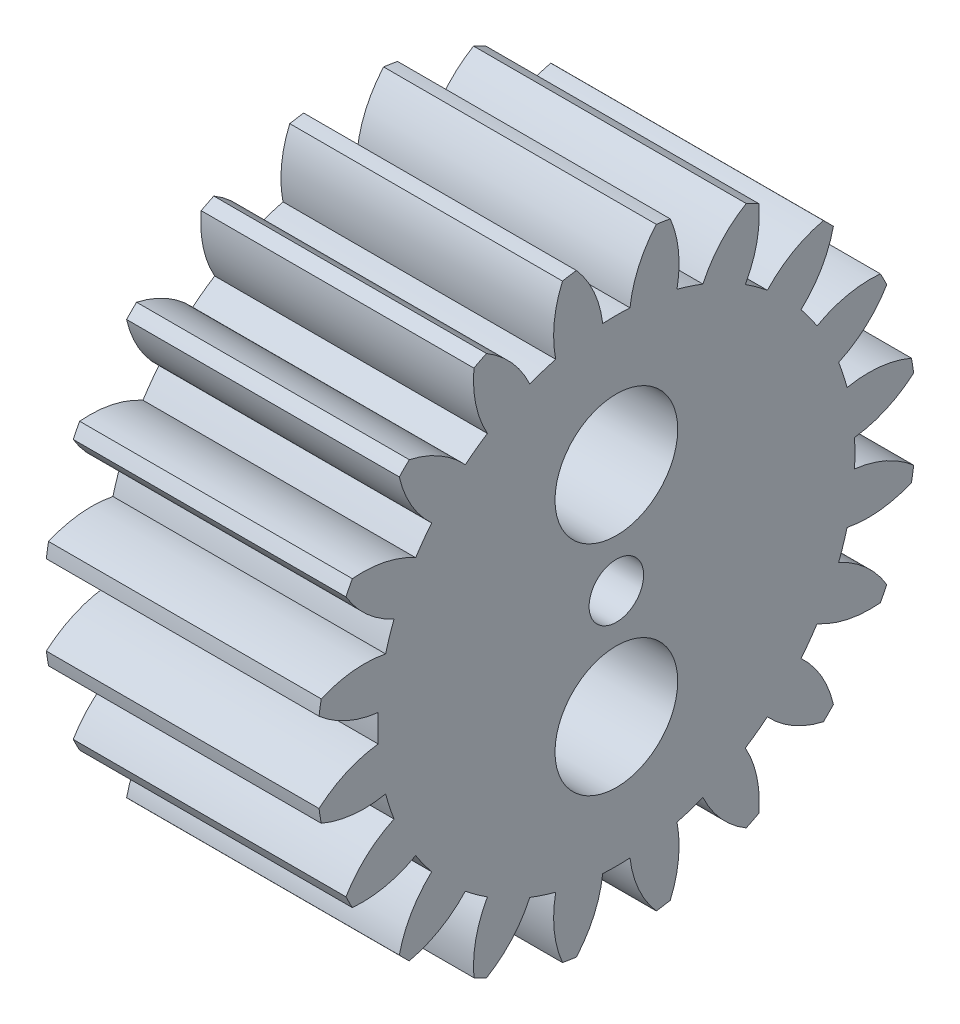
SolidWorks part; units mm, degrees
ref_plane "Plane1" through (0, 0, 0) normal (0, 0, 1) x (1, 0, 0)
ref_plane "Plane2" through (0, 0, 0) normal (0, 1, 0) x (1, 0, 0)
ref_plane "Plane3" through (0, 0, 0) normal (1, 0, 0) x (0, 0, -1)
sketch "HoldingSke" plane through (0, 0, 0) normal (0, 1, 0) x (1, 0, 0)
  line L0 (0, 0) -> (1.8794, -0.684)
  line L1 (-15, 0) -> (100, 0) construction
  line L2 (0, 0) -> (-2.1039, 2.3779)
  line L3 (0, 0) -> (-11.863, 4.5341)
  line L4 (0, 0) -> (8.1152, 2.9537)
  line L5 (0, 0) -> (-46.8476, -17.4728)
  line L6 (0, 0) -> (-4.1448, -2.7965)
  line L7 (-2.1039, 2.3779) -> (8.6586, 51.2059)
  line L8 (-76.2, 54.61) -> (-76.1, 54.61)
  line L9 (-71.009, 38.7566) -> (-53.1078, 45.2721)
  line L10 (-76.2, 71.12) -> (104.1128, 71.12)
  line L11 (0, 0) -> (-5, 0)
  line L12 (-76.2, 101.6) -> (-76.181, 101.6)
  line L13 (24.9733, 27.94) -> (52.9518, 28.4284)
  line L14 (24.9733, 27.94) -> (24.9743, 27.94)
  line L15 (24.9733, 27.94) -> (100.4006, 29.5858)
  line L16 (-63.627, -0.5) -> (-12.827, -0.5)
  circle A0 centre (0, 0) radius 0.5
  circle A1 centre (0, 0) radius 4.374
  circle A2 centre (0, 0) radius 37.5
  circle A3 centre (0, 0) radius 0.5
  dimension "MHD" = 8.748
  dimension "Hub_dia" = 75
  dimension "Bore" = 1
  dimension "MBD" = 1
  dimension "Num_teeth" = 20
  dimension "Pitch" = 2
  dimension "Overall_len" = 50
  dimension "Show_teeth" = 20
  dimension "Thickness" = 5
  dimension "OAL" = 50.0001
  dimension "T_dim" = 0.1
  dimension "Ap" = 20
  dimension "H" = 19.05
  dimension "Pitch_radius" = 180.3128
  dimension "Width" = 5
  dimension "Backlash" = 0.019
  dimension "Addendum_fac" = 1
  dimension "Dedendum_fac" = 1.25
  dimension "Clearance_fac" = 0.25
  dimension "Dedendum_add" = 0.001
  dimension "Module" = 0.5
sketch "BasProSke" plane through (0, 0, 0) normal (0, 1, 0) x (1, 0, 0)
  line L0 (-10, 0) -> (60, 0) construction
  line L1 (0, 0) -> (0, 5.5)
  line L2 (0, 0) -> (5, 0)
  line L3 (5, 0) -> (5, 5.5)
  line L4 (5, 5.5) -> (0, 5.5)
  dimension "Thickness" = 5
  dimension "Diameter" = 11
revolve "Base-Revolve" add sketch "BasProSke" angle 360 about L0
sketch "TooCutSke" plane through (0, 0, 0) normal (1, 0, 0) x (0, 0, -1)
  line L1 (0, 0) -> (0, 107) construction
  line L2 (0, 0) -> (-0.4255, 4.9819) construction
  line L3 (0, 0) -> (-1.5603, 9.8514) construction
  line L4 (-0.4255, 4.9819) -> (-0.7802, 4.9257) construction
  arc A0 (0.2499, 4.3669) -> (-0.2499, 4.3669) centre (0, 0) ccw
  arc A1 (0.7528, 5.4739) -> (-0.7528, 5.4739) centre (0, 0) ccw
  circle A2 centre (0, 0) radius 5 construction
  circle A3 centre (0, 0) radius 4.6985 construction
  arc A4 (-0.2499, 4.3669) -> (-0.7528, 5.4739) centre (-2.2361, 4.1322) ccw
  arc A5 (0.7528, 5.4739) -> (0.2499, 4.3669) centre (2.2361, 4.1322) ccw
  dimension "Root_dia" = 8.748
  dimension "Overcut_dia" = 11.0508
  dimension "Pitch_dia" = 10
  dimension "Base_dia" = 9.3969
  dimension "Flank_rad" = 2
  dimension "Half_ang" = 9
  dimension "Half_CT" = 0.359
extrude "ToothCut" cut sketch "TooCutSke" along normal through all
fillet "Breaks" [suppressed] radius 0.01
fillet "RootFillets" [suppressed] radius 0.126
pattern_circular "TeethCuts" count 20 every 18 about axis through (-10, 0, 0) along (1, 0, 0) of "ToothCut", "RootFillets", "Breaks"
sketch "HubNeaOneSke" plane through (0, 0, 0) normal (-1, 0, 0) x (0, 0, 1)
  circle A0 centre (0, 0) radius 4.374
  dimension "Diameter" = 8.748
extrude "HubNearOne" [suppressed] add sketch "HubNeaOneSke" along normal blind 45.0001
sketch "HubNeaBotSke" plane through (0, 0, 0) normal (-1, 0, 0) x (0, 0, 1)
  circle A0 centre (0, 0) radius 4.374
  dimension "Diameter" = 8.748
extrude "HubNearBoth" [suppressed] add sketch "HubNeaBotSke" along normal blind 22.5
ref_plane "FarPln" through (5, 0, 0) normal (1, 0, 0) x (0, 0, -1)
sketch "HubFarSke" plane through (5, 0, 0) normal (1, 0, 0) x (0, 0, -1)
  circle A0 centre (0, 0) radius 4.374
  dimension "Diameter" = 8.748
extrude "HubFar" [suppressed] add sketch "HubFarSke" along normal blind 22.5
sketch "BorSke" plane through (0, 0, 0) normal (1, 0, 0) x (0, 0, -1)
  circle A0 centre (0, 0) radius 0.5
  dimension "Diameter" = 1
extrude "Bore" cut sketch "BorSke" along normal mid plane 100.0001
sketch "KeySke" plane through (0, 0, 0) normal (1, 0, 0) x (0, 0, -1)
  line L0 (-0.05, 0) -> (-0.05, 0.6)
  line L1 (-0.05, 0.6) -> (0.05, 0.6)
  line L2 (0.05, 0.6) -> (0.05, 0)
  line L3 (0, 0) -> (0, 34) construction
  line L4 (-0.05, 0) -> (0.05, 0)
  dimension "Offset" = 0.6
  dimension "Width" = 0.1
extrude "Keyway" [suppressed] cut sketch "KeySke" along normal mid plane 100.0001
pattern_circular "Keyway2" [suppressed] count 2 every 90 about axis through (-10, 0, 0) along (1, 0, 0)
sketch "Sketch1" plane through (5, 0, 0) normal (1, 0, 0) x (0, 0, -1)
  line L0 (0, 4.374) -> (0, -4.374) construction
  arc A0 (0.2499, 4.3669) -> (-0.2499, 4.3669) centre (0, 0) ccw construction
  arc A1 (-0.2499, -4.3669) -> (0.2499, -4.3669) centre (0, 0) ccw construction
  circle A2 centre (0, 2) radius 1.125
  circle A3 centre (0, -2) radius 1.125
  circle A4 centre (0, 0) radius 0.5 construction
  dimension "D1" = 2.25
  dimension "D2" = 2
  dimension "D3" = 2
extrude "Cut-Extrude1" cut sketch "Sketch1" against normal through all both and the other way through all
equation "' \"Module@HoldingSke\" = 6.35"
equation "' \"Num_teeth@HoldingSke\" = 12"
equation "' \"Ap@HoldingSke\" =  20"
equation "' \"Ap@HoldingSke\" = 20"
equation "' \"Width@HoldingSke\" = 0.5 * 25.4"
equation "' \"Hub_dia@HoldingSke\"= 1 * 25.4"
equation "' \"Hub_dia@HoldingSke\" = 1 * 25.4"
equation "' \"Overall_len@HoldingSke\" = 1.0 * 25.4"
equation "' \"Bore@HoldingSke\" = 0.75 * 25.4"
equation "' \"T_dim@HoldingSke\" = 0.1 * 25.4"
equation "' \"Width@KeySke\" = 0.25 * 25.4"
equation "' \"Show_teeth@HoldingSke\" = 13"
equation "' \"Backlash@HoldingSke\" = 0.009 * 25.4"
equation "' \"Addendum_fac@HoldingSke\" = 1.0"
equation "' \"Dedendum_fac@HoldingSke\" = 1.25"
equation "' \"Dedendum_add@HoldingSke\" = 0.00005 * 25.4"
equation "' \"Clearance_fac@HoldingSke\" = 0.25"
equation "\"Pitch@HoldingSke\" = 1 / \"Module@HoldingSke\""
equation "\"Overcut_dia@TooCutSke\" = (\"Num_teeth@HoldingSke\" + 2 * \"Addendum_fac@HoldingSke\") / \"Pitch@HoldingSke\" + 0.002 * 25.4"
equation "\"Pitch_dia@TooCutSke\" = \"Num_teeth@HoldingSke\" / \"Pitch@HoldingSke\""
equation "\"Base_dia@TooCutSke\" = \"Num_teeth@HoldingSke\" / \"Pitch@HoldingSke\" * cos((\"Ap@HoldingSke\"  * 3.14159265 / 180))"
equation "\"Root_dia@TooCutSke\" = (\"Num_teeth@HoldingSke\" + 2) / \"Pitch@HoldingSke\" - 2 * (\"Addendum_fac@HoldingSke\" + \"Dedendum_fac@HoldingSke\") / \"Pitch@HoldingSke\" - \"Dedendum_add@HoldingSke\" * 2"
equation "\"Half_ang@TooCutSke\" = 180 / \"Num_teeth@HoldingSke\""
equation "\"Half_CT@TooCutSke\" = \"Num_teeth@HoldingSke\" / \"Pitch@HoldingSke\" * sin((3.14159265 / 2 / \"Num_teeth@HoldingSke\")) / 2 - 7 * \"Backlash@HoldingSke\" / 4"
equation "\"Flank_rad@TooCutSke\" = \"Num_teeth@HoldingSke\" / \"Pitch@HoldingSke\" / 5"
equation "\"Radius@RootFillets\" = \"Clearance_fac@HoldingSke\" / \"Pitch@HoldingSke\" + \"Dedendum_add@HoldingSke\""
equation "\"Break_rad@Breaks\" = 0.02 / \"Pitch@HoldingSke\""
equation "\"Thickness@HoldingSke\" = \"Width@HoldingSke\""
equation "\"OAL@HoldingSke\" = \"Thickness@HoldingSke\""
equation "\"MHD@HoldingSke\" = (\"Num_teeth@HoldingSke\" + 2) / \"Pitch@HoldingSke\" - 2 * (\"Addendum_fac@HoldingSke\" + \"Dedendum_fac@HoldingSke\")  / \"Pitch@HoldingSke\" - \"Dedendum_add@HoldingSke\" * 2"
equation "\"MBD@HoldingSke\" = (\"Num_teeth@HoldingSke\" + 2) / \"Pitch@HoldingSke\" - 2 * (\"Addendum_fac@HoldingSke\" + \"Dedendum_fac@HoldingSke\")  / \"Pitch@HoldingSke\" - \"Dedendum_add@HoldingSke\" * 2 - 0.002 * 25.4"
equation "\"MHD@HoldingSke\" = ((sgn( \"MHD@HoldingSke\" - \"Hub_dia@HoldingSke\" )-1)*( \"MHD@HoldingSke\" - \"Hub_dia@HoldingSke\" ))/-2+ \"Hub_dia@HoldingSke\""
equation "\"MBD@HoldingSke\" = ((sgn( \"MBD@HoldingSke\" - \"Bore@HoldingSke\" )-1)*( \"MBD@HoldingSke\" - \"Bore@HoldingSke\" ))/-2+ \"Bore@HoldingSke\""
equation "\"OAL@HoldingSke\" = ((sgn( \"OAL@HoldingSke\" - \"Overall_len@HoldingSke\" )+1)*( \"OAL@HoldingSke\" - \"Overall_len@HoldingSke\" ))/2 + \"Overall_len@HoldingSke\" + 0.000002 * 25.4"
equation "\"Num_teeth@TeethCuts\" = int( \"Show_teeth@HoldingSke\" ) + 1"
equation "\"Num_teeth@TeethCuts\" = ((sgn( \"Num_teeth@TeethCuts\" - \"Num_teeth@HoldingSke\" )-1)*( \"Num_teeth@TeethCuts\" - \"Num_teeth@HoldingSke\" ))/-2+ \"Num_teeth@HoldingSke\""
equation "\"Num_teeth@TeethCuts\" = ((sgn( \"Num_teeth@TeethCuts\" - 2.0)+1)*( \"Num_teeth@TeethCuts\" - 2.0))/2 +2.0"
equation "\"Angle@TeethCuts\" = 360.0 / \"Num_teeth@HoldingSke\""
equation "\"Diameter@BasProSke\" = (\"Num_teeth@HoldingSke\" + 2 * \"Addendum_fac@HoldingSke\") / \"Pitch@HoldingSke\""
equation "\"Thickness@BasProSke\"  = \"Thickness@HoldingSke\""
equation "' \"Fillet_rad@BasProSke\" =  \"Thickness@HoldingSke\" * 0.05"
equation "' \"Fillet_rad@BasProSke\" = \"Thickness@HoldingSke\" * 0.05"
equation "\"MHD@HoldingSke\" = ((sgn( \"MHD@HoldingSke\" - \"Root_dia@TooCutSke\" )-1)*( \"MHD@HoldingSke\" - \"Root_dia@TooCutSke\" ))/-2+ \"Root_dia@TooCutSke\""
equation "\"Diameter@HubNeaOneSke\" = \"MHD@HoldingSke\""
equation "\"Length@HubNearOne\" = \"OAL@HoldingSke\" - \"Thickness@BasProSke\""
equation "\"Diameter@HubNeaBotSke\" = \"MHD@HoldingSke\""
equation "\"Length@HubNearBoth\" = ( \"OAL@HoldingSke\" - \"Thickness@BasProSke\" ) / 2.0"
equation "\"Thickness@FarPln\" = \"Thickness@BasProSke\""
equation "\"Diameter@HubFarSke\" = \"MHD@HoldingSke\""
equation "\"Length@HubFar\" = ( \"OAL@HoldingSke\" - \"Thickness@BasProSke\" ) / 2.0"
equation "\"Diameter@BorSke\" = \"MBD@HoldingSke\""
equation "\"D1@Bore\" = \"OAL@HoldingSke\" * 2.0"
equation "\"D1@Keyway\" = \"OAL@HoldingSke\" * 2.0"
equation "\"Offset@KeySke\" = \"T_dim@HoldingSke\" + \"MBD@HoldingSke\" / 2.0"
